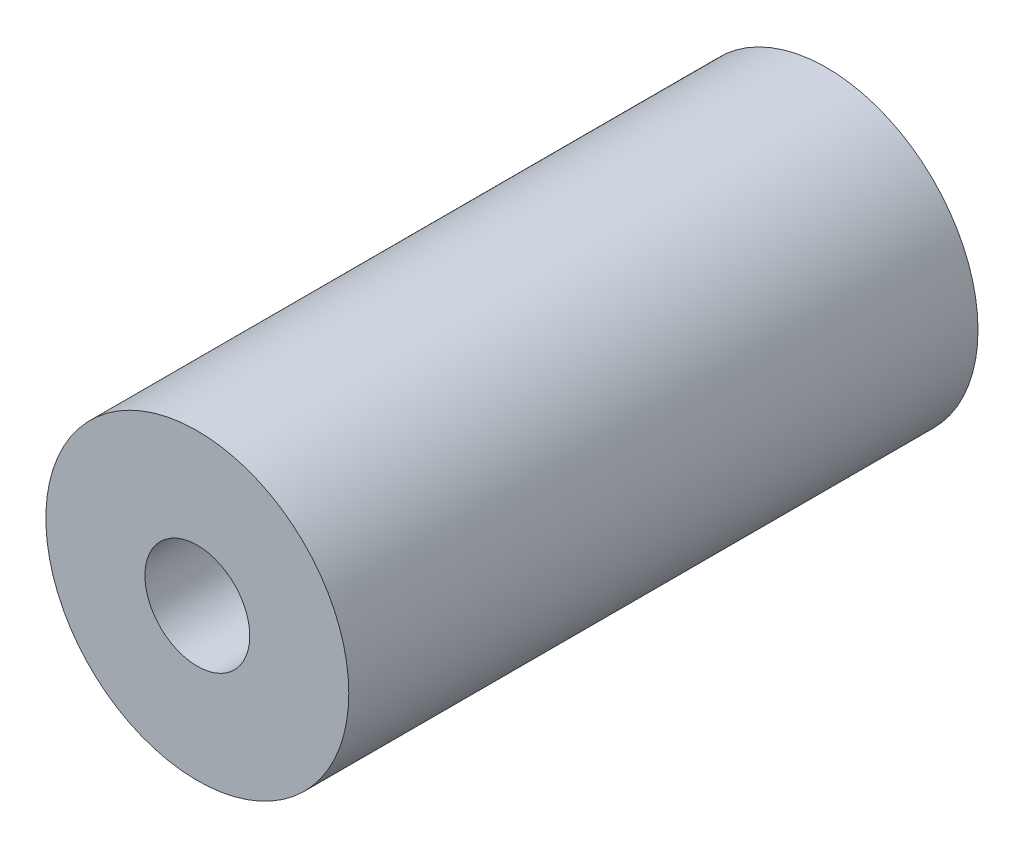
SolidWorks part; units mm, degrees
ref_plane "Front Plane" through (0, 0, 0) normal (0, 0, 1) x (1, 0, 0)
ref_plane "Top Plane" through (0, 0, 0) normal (0, 1, 0) x (1, 0, 0)
ref_plane "Right Plane" through (0, 0, 0) normal (1, 0, 0) x (0, 0, -1)
sketch "Sketch1" plane through (0, 0, 0) normal (0, 0, 1) x (1, 0, 0)
  circle A0 centre (0, 0) radius 13
  circle A1 centre (0, 0) radius 4.5
extrude "Boss-Extrude1" add sketch "Sketch1" along normal blind 54
